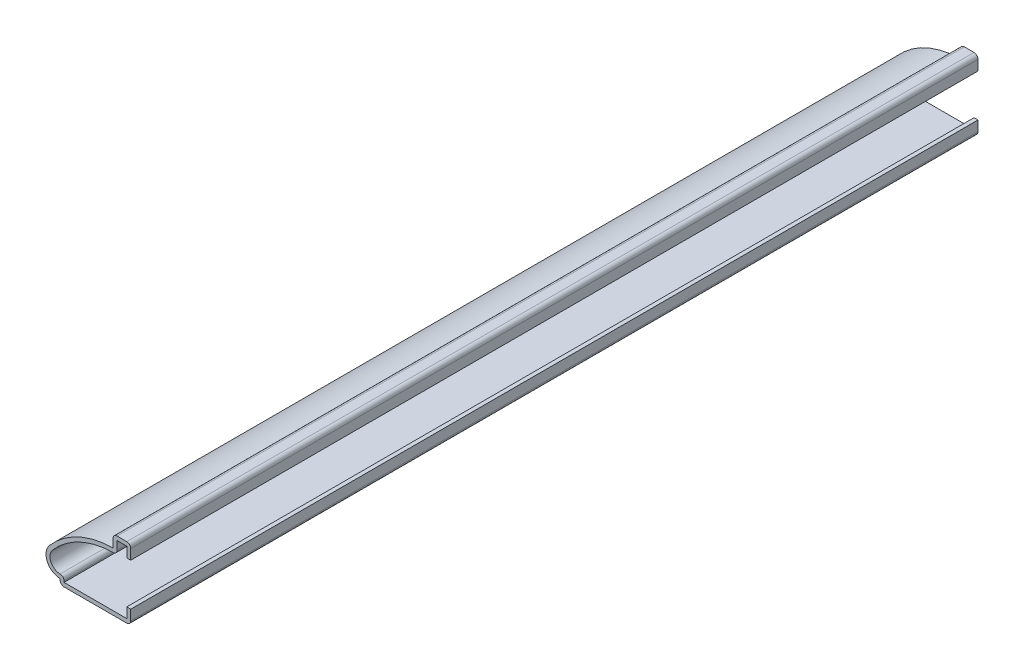
SolidWorks part; units mm, degrees
ref_plane "Front Plane" through (0, 0, 0) normal (0, 0, 1) x (1, 0, 0)
ref_plane "Top Plane" through (0, 0, 0) normal (0, 1, 0) x (1, 0, 0)
ref_plane "Right Plane" through (0, 0, 0) normal (1, 0, 0) x (0, 0, -1)
sketch "Sketch1" plane through (0, 0, 0) normal (0, 0, 1) x (1, 0, 0)
  line L0 (0, 0) -> (0, -3.175)
  line L1 (0, -3.175) -> (-15.875, -3.175)
  line L2 (-15.875, -3.175) -> (-15.875, -1.9844)
  line L3 (-3.9688, 9.9219) -> (-3.9688, 12.7)
  line L4 (-3.9688, 12.7) -> (0, 12.7)
  line L5 (0, 12.7) -> (0, 9.525)
  arc A0 (-15.875, -1.9844) -> (-18.2879, 3.2542) centre (-15.875, 1.1906) cw
  arc A1 (-18.2879, 3.2542) -> (-3.9688, 9.9219) centre (-3.8105, -9.1275) cw
  point P11 (0, 11.5783)
  point P13 (0, 0)
  point P14 (0, 0)
  dimension "D12" = 19.05
  dimension "D1" = 3.175
  dimension "D2" = 15.875
  dimension "D3" = 1.1906
  dimension "D4" = 3.175
  dimension "D5" = 3.175
  dimension "D6" = 3.9688
  dimension "D7" = 15.0813
  dimension "D8" = 19.05
  dimension "D9" = 2.7781
  dimension "D10" = 15.875
  dimension "D11" = 9.525
extrude "Extrude-Thin1" add sketch "Sketch1" against normal blind 190.5 thin
fillet "Fillet1" radius 0.889 6 edges at (0, -3.175, -95.25) (-15.875, -3.175, -95.25) (-14.986, -0.9154, -95.25) (-3.0798, 9.0188, -95.25) (-3.9688, 12.7, -95.25) (0, 12.7, -95.25)
